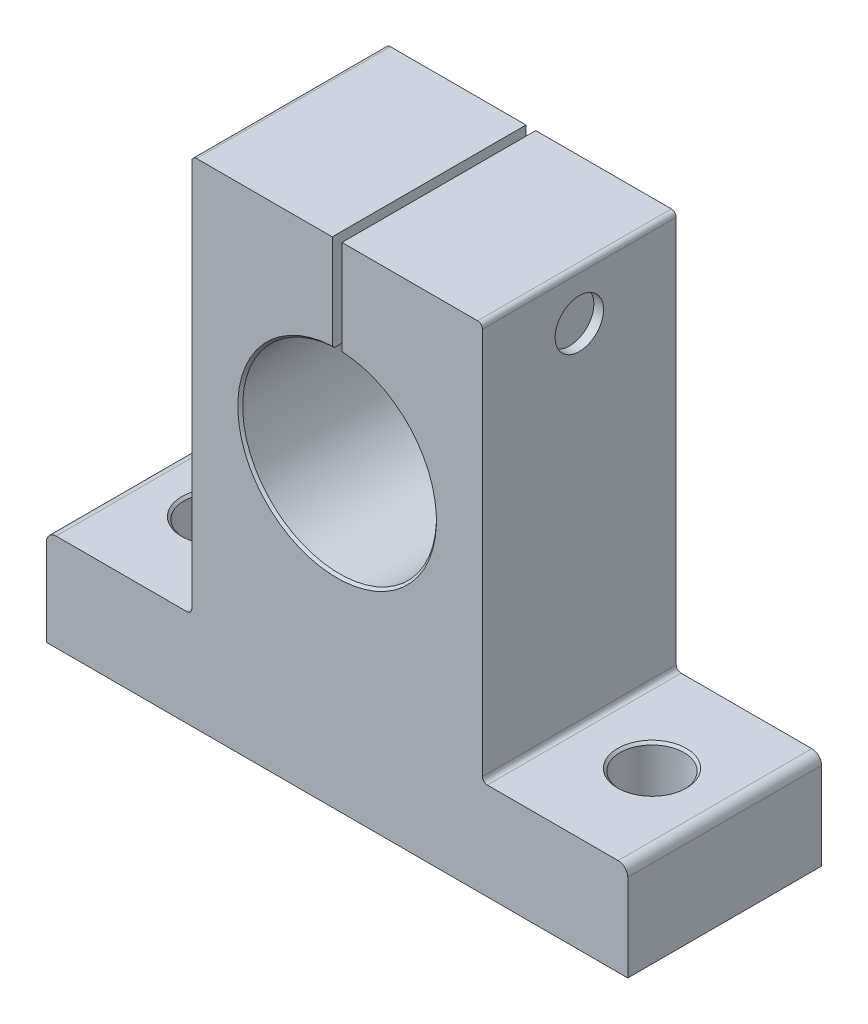
SolidWorks part; units mm, degrees
ref_plane "Front Plane" through (0, 0, 0) normal (0, 0, 1) x (1, 0, 0)
ref_plane "Top Plane" through (0, 0, 0) normal (0, 1, 0) x (1, 0, 0)
ref_plane "Right Plane" through (0, 0, 0) normal (1, 0, 0) x (0, 0, -1)
sketch "Sketch1" plane through (0, 0, 0) normal (0, 0, 1) x (1, 0, 0)
  line L0 (-30, 0) -> (30, 0)
  line L1 (-30, 0) -> (-30, 10)
  line L2 (-30, 10) -> (-15, 10)
  line L3 (-15, 10) -> (-15, 51)
  line L4 (-15, 51) -> (-0.5, 51)
  line L5 (15, 51) -> (15, 10)
  line L6 (15, 10) -> (30, 10)
  line L7 (30, 10) -> (30, 0)
  line L8 (-0.5, 51) -> (-0.5, 40.9875)
  line L9 (0.5, 51) -> (0.5, 40.9875)
  line L10 (0.5, 51) -> (15, 51)
  arc A0 (-0.5, 40.9875) -> (0.5, 40.9875) centre (0, 31) ccw
  point P11 (0, 0)
  point P13 (-0.5, 45.9937)
  dimension "D6" = 10
  dimension "D1" = 60
  dimension "D2" = 10
  dimension "D3" = 31
  dimension "D4" = 51
  dimension "D5" = 1
  dimension "D7" = 30
extrude "Boss-Extrude1" add sketch "Sketch1" along normal blind 20
sketch "Sketch3" plane through (0, 0, 0) normal (0, -1, 0) x (1, 0, 0)
  line L0 (-22.5, 10) -> (22.5, 10) construction
  line L1 (-30, 20) -> (-30, 0) construction
  circle A0 centre (-22.5, 10) radius 3.3
  circle A1 centre (22.5, 10) radius 3.3
  point P2 (0, 10)
  point P7 (-30, 10)
  dimension "D2" = 6.6
  dimension "D1" = 45
extrude "Cut-Extrude1" cut sketch "Sketch3" against normal blind 10 and the other way through all
fillet "Fillet1" radius 1 2 edges at (30, 10, 10) (-30, 10, 10)
fillet "Fillet2" radius 0.5 4 edges at (-15, 51, 10) (15, 51, 10) (15, 10, 10) (-15, 10, 10)
chamfer "Chamfer1" distance 0.25 6 edges at (-22.5, 0, 13.3) (22.5, 0, 13.3) (25.8, 10, 10) (-19.2, 10, 10) (0, 21, 0) (0, 21, 20)
sketch "Sketch4" plane through (-15, 0, 0) normal (-1, 0, 0) x (0, 0, 1)
  line L0 (20, 50.5) -> (0, 50.5) construction
  line L1 (0, 51) -> (20, 51) construction
  circle A0 centre (10, 46) radius 3.85
  point P6 (10, 50.5)
  dimension "D1" = 7.7
  dimension "D2" = 5
extrude "Cut-Extrude2" cut sketch "Sketch4" against normal blind 1
sketch "Sketch5" plane through (-14, 0, 0) normal (-1, 0, 0) x (0, 0, 1)
  circle A0 centre (10, 46) radius 3.85
  circle A1 centre (10, 46) radius 3.75
  dimension "D1" = 7.5
  dimension "D2" = 7.7
extrude "Cut-Extrude3" cut sketch "Sketch5" against normal blind 5
chamfer "Chamfer2" distance 0.25 1 edges at (-14, 42.25, 10)
sketch "Sketch6" plane through (-14, 0, 0) normal (-1, 0, 0) x (0, 0, 1)
  line L1 (9.8557, 43.8398) -> (11.7987, 44.7949)
  line L2 (11.7987, 44.7949) -> (11.943, 46.9551)
  line L3 (11.943, 46.9551) -> (10.1443, 48.1602)
  line L4 (10.1443, 48.1602) -> (8.2013, 47.2051)
  line L5 (8.2013, 47.2051) -> (8.057, 45.0449)
  line L6 (8.057, 45.0449) -> (9.8557, 43.8398)
  circle A0 centre (10, 46) radius 1.875 construction
  dimension "D1" = 3.75
extrude "Cut-Extrude4" cut sketch "Sketch6" against normal blind 2.5
sketch "Sketch7" plane through (-0.5, 0, 0) normal (1, 0, 0) x (0, 0, -1)
  circle A0 centre (-10, 46) radius 2.5
  dimension "D1" = 5
extrude "Boss-Extrude2" add sketch "Sketch7" along normal blind 1
sketch "Sketch8" plane through (15, 0, 0) normal (1, 0, 0) x (0, 0, -1)
  circle A0 centre (-10, 46) radius 2.5
  dimension "D1" = 5
extrude "Cut-Extrude5" cut sketch "Sketch8" against normal blind 1
sketch "Sketch9" plane through (-14, 0, 0) normal (-1, 0, 0) x (0, 0, 1)
  circle A0 centre (10, 46) radius 2.1651
extrude "Cut-Extrude6" cut sketch "Sketch9" against normal blind 1 draft 45
equation "\"h\"= 31'6"
equation "\"w\"= 60'1"
equation "\"l\"= 20'3"
equation "\"f\"= 51'2"
equation "\"g\"= 10'9"
equation "\"p\"= 30'5"
equation "\"b\"= 45'4"
equation "\"s\"= 6.6'10"
equation "\"sk\"= 20'7 dg kinh truc"
equation "\"D1@Sketch1\"=\"w\""
equation "\"D2@Sketch1\"=\"g\""
equation "\"D3@Sketch1\"=\"h\""
equation "\"D4@Sketch1\"=\"f\""
equation "\"rk\"= 1'11 be rong khe"
equation "\"D5@Sketch1\"=\"rk\""
equation "\"D6@Sketch1\"=\"sk\"/2"
equation "\"D1@Boss-Extrude1\"=\"l\""
equation "\"D1@Sketch3\"=\"b\""
equation "\"D2@Sketch3\"=\"s\""
equation "\"D1@Cut-Extrude1\"=\"g\""
equation "\"D7@Sketch1\"=\"p\""
equation "\"bo\"= 1'12 bo goc"
equation "\"D1@Fillet1\"=\"bo\""
equation "\"D1@Fillet2\"=\"bo\"/2"
equation "\"D1@Chamfer1\"=\"bo\"/4"
equation "\"m\"= 5'8 bu long"
equation "\"D1@Sketch4\"=1.5*\"m\"+0.2"
equation "\"D1@Sketch5\"=\"m\"*1.5"
equation "\"D2@Sketch5\"=\"m\"*1.5+0.2"
equation "\"D1@Cut-Extrude3\"=\"m\""
equation "\"D1@Chamfer2\"=\"m\"*0.05"
equation "\"D1@Cut-Extrude4\"=\"m\"/2"
equation "\"D1@Sketch6\"=\"m\"*3/4"
equation "\"D1@Sketch7\"=\"m\""
equation "\"D1@Boss-Extrude2\"=\"rk\""
equation "\"D1@Sketch8\"=\"m\""
equation "\"D2@Sketch4\"=(\"f\"-\"h\"-\"sk\"/2)/2"
